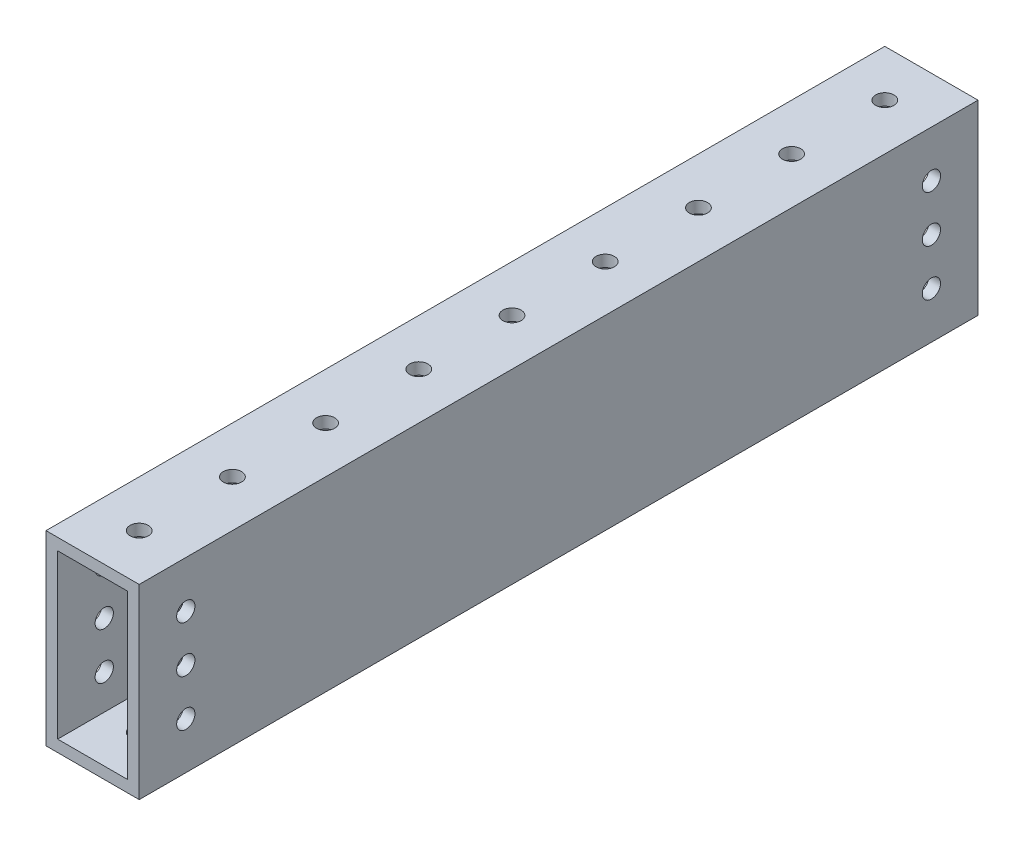
SolidWorks part; units mm, degrees
material "6061-T6 (SS)"
ref_plane "Front Plane" through (0, 0, 0) normal (0, 0, 1) x (1, 0, 0)
ref_plane "Top Plane" through (0, 0, 0) normal (0, 1, 0) x (1, 0, 0)
ref_plane "Right Plane" through (0, 0, 0) normal (1, 0, 0) x (0, 0, -1)
sketch "Sketch1" plane through (0, 0, 0) normal (0, 0, 1) x (1, 0, 0)
  line L0 (-9.525, 22.225) -> (9.525, 22.225)
  line L1 (-12.7, 25.4) -> (12.7, 25.4)
  line L2 (-12.7, 25.4) -> (-12.7, -25.4)
  line L3 (-12.7, -25.4) -> (12.7, -25.4)
  line L4 (12.7, 25.4) -> (12.7, -25.4)
  line L5 (9.525, 22.225) -> (9.525, -22.225)
  line L6 (-9.525, -22.225) -> (9.525, -22.225)
  line L7 (-9.525, 22.225) -> (-9.525, -22.225)
  line L8 (-12.7, 25.4) -> (12.7, -25.4) construction
  line L9 (12.7, 25.4) -> (-12.7, -25.4) construction
  point P5 (0, 0)
  dimension "D1" = 25.4
  dimension "D2" = 50.8
  dimension "D3" = 3.175
extrude "Boss-Extrude1" add sketch "Sketch1" along normal mid plane 228.6
sketch "Sketch2" plane through (0, 25.4, 0) normal (0, 1, 0) x (1, 0, 0)
  line L4 (12.7, -114.3) -> (-12.7, -114.3) construction
  circle A64 centre (0, -101.6) radius 2.4892
  circle A65 centre (0, -76.2) radius 2.4892
  circle A66 centre (0, -50.8) radius 2.4892
  circle A67 centre (0, -25.4) radius 2.4892
  circle A68 centre (0, 0) radius 2.4892
  circle A69 centre (0, 25.4) radius 2.4892
  circle A70 centre (0, 50.8) radius 2.4892
  circle A71 centre (0, 76.2) radius 2.4892
  circle A72 centre (0, 101.6) radius 2.4892
  dimension "D2" = 12.7
  dimension "D4" = 25.4
  dimension "D1" = 4.9784
  dimension "D3" = 9
extrude "Cut-Extrude1" cut sketch "Sketch2" against normal through all
sketch "Sketch3" plane through (-12.7, 0, 0) normal (-1, 0, 0) x (0, 0, 1)
  line L0 (101.6, -25.4) -> (101.6, 25.4) construction
  line L1 (114.3, -25.4) -> (-114.3, -25.4) construction
  line L2 (114.3, 25.4) -> (-114.3, 25.4) construction
  line L3 (114.3, 25.4) -> (114.3, -25.4) construction
  circle A0 centre (101.6, 0) radius 2.4892
  circle A1 centre (101.6, -12.7) radius 2.4892
  circle A2 centre (101.6, 12.7) radius 2.4892
  dimension "D2" = 4.9784
  dimension "D4" = 12.7
  dimension "D1" = 12.7
  dimension "D3" = 12.7
extrude "Cut-Extrude2" cut sketch "Sketch3" against normal through all
mirror "Mirror1" about plane through (0, 0, 0) normal (0, 0, 1) of "Cut-Extrude2"
